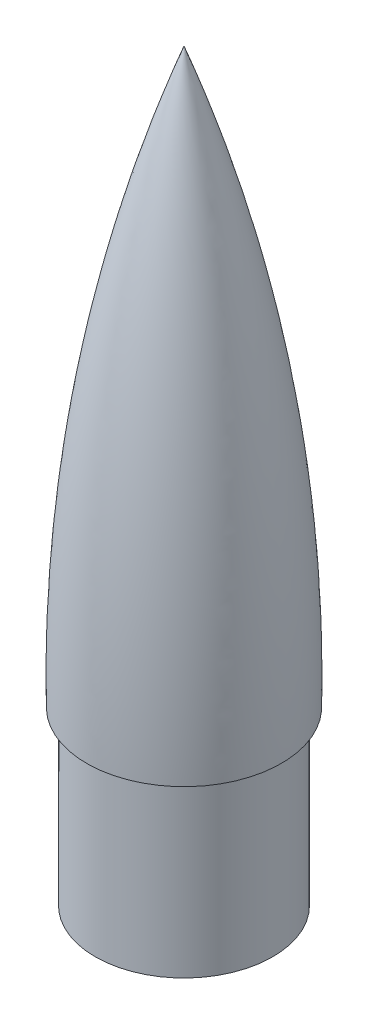
SolidWorks part; units mm, degrees
ref_plane "Спереди" through (0, 0, 0) normal (0, 0, 1) x (1, 0, 0)
ref_plane "Сверху" through (0, 0, 0) normal (0, 1, 0) x (1, 0, 0)
ref_plane "Справа" through (0, 0, 0) normal (1, 0, 0) x (0, 0, -1)
sketch "Эскиз1" plane through (0, 0, 0) normal (0, 1, 0) x (1, 0, 0)
  circle A0 centre (0, 0) radius 14.5
  circle A1 centre (0, 0) radius 15.5
  dimension "D1" = 31
  dimension "D2" = 29
extrude "Бобышка-Вытянуть1" add sketch "Эскиз1" along normal blind 30
sketch "Эскиз5" plane through (0, 0, 0) normal (0, 0, 1) x (1, 0, 0)
  line L0 (0, 100) -> (0, 0) construction
  line L1 (0, 30) -> (0, 130)
  line L2 (0, 30) -> (-17, 30)
  line L3 (15.5, 30) -> (-15.5, 30) construction
  arc A1 (0, 130) -> (-17, 30) centre (257.5302, 34.7749) ccw
revolve "Повернуть1" add sketch "Эскиз5" angle 360 about L0
sketch "Эскиз6" plane through (0, 0, 0) normal (0, 0, 1) x (1, 0, 0)
  line L2 (0, 127.5) -> (-1.2853, 123.6776) construction
  line L3 (-1.2853, 123.6776) -> (-2.1438, 120.7719) construction
  line L9 (-2.1438, 120.7719) -> (-5.6376, 103.8091) construction
  line L20 (0, 30) -> (0, 130) construction
  line L21 (0, 127.5) -> (0, 30)
  line L22 (-2.5, 32.5) -> (-2.5, 114.8206)
  line L23 (-14.532, 32.5) -> (-2.5, 32.5)
  line L26 (0, 30) -> (-15, 30)
  line L27 (0, 30) -> (-17, 30) construction
  line L28 (-14.4536, 41.6899) -> (-14.5645, 36.7098) construction
  line L29 (-14.5645, 36.7098) -> (-15, 30) construction
  arc A5 (-2.5, 114.8206) -> (-14.532, 32.5) centre (257.5302, 34.7749) ccw
  arc A6 (-5.6376, 103.8091) -> (-14.4536, 41.6899) centre (257.5302, 34.7749) ccw
  spline S0 degree 2 poles (-14.4536, 41.6899) (-14.5645, 36.7098) (-15, 30) knots 0 0 0 1 1 1
  spline S1 degree 3 poles (0, 127.5) (-1.2853, 123.6776) (-2.1438, 120.7719) (-5.6376, 103.8091) knots 0 0 0 0 1 1 1 1
  point P0 (0, 127.5)
  dimension "D2" = 2.5
  dimension "D3" = 2
  dimension "D1" = 2.5
revolve "Вырез-Повернуть1" cut sketch "Эскиз6" angle 360 about L21
sketch "Эскиз7" plane through (0, 0, 0) normal (0, 0, 1) x (1, 0, 0)
  line L0 (-15.5, 0) -> (15.5, 0) construction
  circle A0 centre (0, 2.5) radius 0.8
  point P0 (0, 0)
  dimension "D1" = 1.6
  dimension "D2" = 2.5
extrude "Вырез-Вытянуть1" cut sketch "Эскиз7" against normal through all
